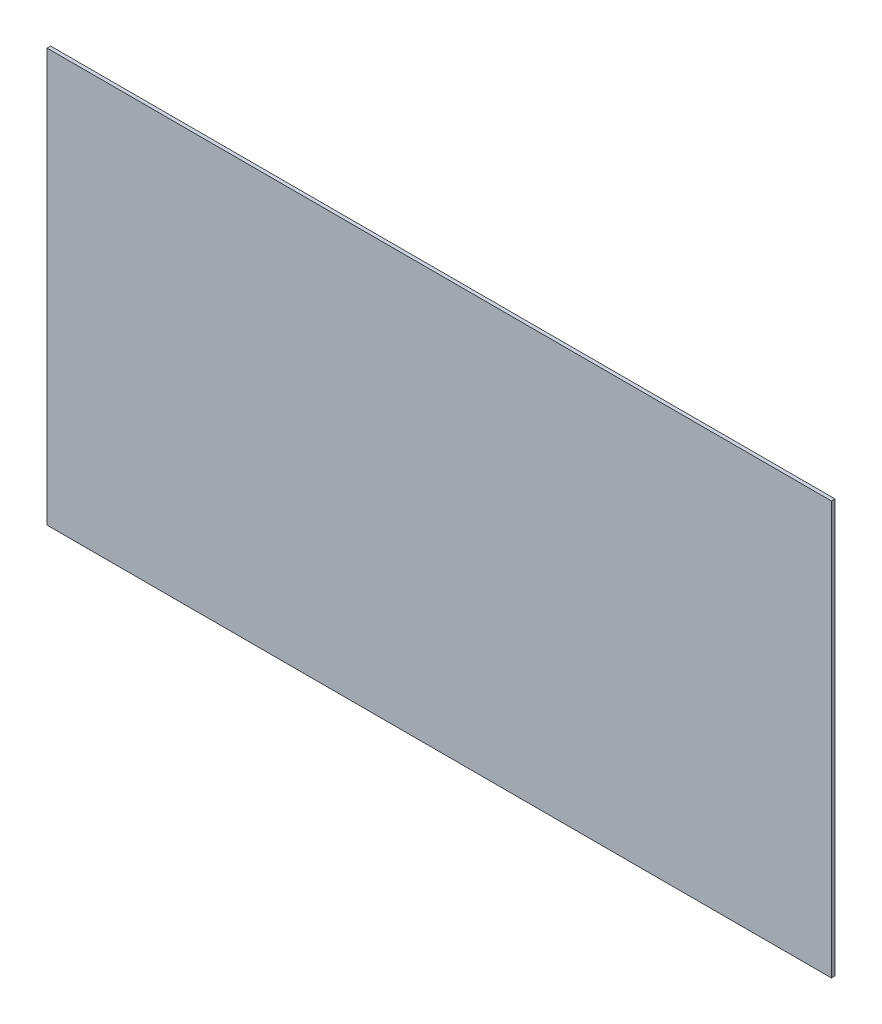
SolidWorks part; units mm, degrees
ref_plane "Front Plane" through (0, 0, 0) normal (0, 0, 1) x (1, 0, 0)
ref_plane "Top Plane" through (0, 0, 0) normal (0, 1, 0) x (1, 0, 0)
ref_plane "Right Plane" through (0, 0, 0) normal (1, 0, 0) x (0, 0, -1)
sketch "Sketch1" plane through (0, 0, 0) normal (0, 0, 1) x (1, 0, 0)
  line L0 (-165.1, 962.43) -> (165.1, 962.43) construction
  line L1 (-165.1, 962.43) -> (165.1, 962.43)
  line L2 (165.1, 788.53) -> (165.1, 962.43) construction
  line L3 (165.1, 788.53) -> (165.1, 962.43)
  line L4 (-165.1, 788.53) -> (-165.1, 962.43) construction
  line L5 (-165.1, 788.53) -> (-165.1, 962.43)
  line L6 (-165.1, 788.53) -> (165.1, 788.53)
extrude "Extrude1" add sketch "Sketch1" along normal mid plane 1.5
